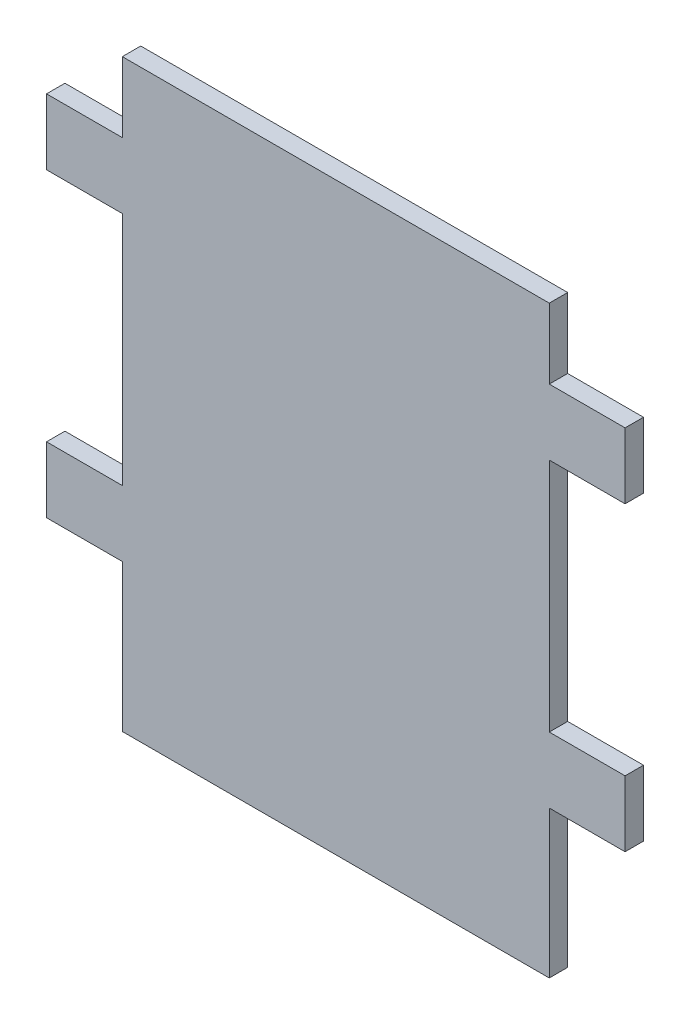
SolidWorks part; units mm, degrees
ref_plane "Front" through (0, 0, 0) normal (0, 0, 1) x (1, 0, 0)
ref_plane "Top" through (0, 0, 0) normal (0, 1, 0) x (1, 0, 0)
ref_plane "Right" through (0, 0, 0) normal (1, 0, 0) x (0, 0, -1)
sketch "Sketch1" plane through (0, 0, 0) normal (0, 0, 1) x (1, 0, 0)
  line L1 (-48.6696, 65.3947) -> (51.1504, 65.3947)
  line L2 (-48.6696, 65.3947) -> (-48.6696, -35.4453)
  line L3 (-48.6696, -35.4453) -> (51.1504, -35.4453)
  line L4 (51.1504, 65.3947) -> (51.1504, -35.4453)
extrude "Boss-Extrude1" add sketch "Sketch1" along normal blind 3.175
sketch "Sketch3" plane through (0, 0, 3.175) normal (0, 0, 1) x (1, 0, 0)
  line L0 (-48.6696, 65.3947) -> (-48.6696, -35.4453) construction
  line L1 (-48.6696, 65.3947) -> (-35.5896, 65.3947)
  line L2 (-48.6696, 65.3947) -> (-48.6696, 53.2946)
  line L3 (-48.6696, 53.2946) -> (-35.5896, 53.2946)
  line L4 (-35.5896, 65.3947) -> (-35.5896, 53.2946)
  line L5 (51.1504, 65.3947) -> (-48.6696, 65.3947) construction
  line L6 (38.0704, 65.3947) -> (51.1504, 65.3947)
  line L7 (-48.6696, 41.9447) -> (-35.5896, 41.9447)
  line L8 (-48.6696, 41.9447) -> (-48.6696, 1.3047)
  line L9 (-48.6696, 1.3047) -> (-35.5896, 1.3047)
  line L10 (-35.5896, 41.9447) -> (-35.5896, 1.3047)
  line L11 (-48.6696, -35.4453) -> (-35.5896, -35.4453)
  line L12 (-48.6696, -35.4453) -> (-48.6696, -10.0453)
  line L13 (-48.6696, -10.0453) -> (-35.5896, -10.0453)
  line L14 (-35.5896, -35.4453) -> (-35.5896, -10.0453)
  line L15 (38.0704, 65.3947) -> (38.0704, 53.2946)
  line L16 (38.0704, 53.2946) -> (51.1504, 53.2946)
  line L17 (51.1504, 65.3947) -> (51.1504, 53.2946)
  line L18 (38.0704, 41.9447) -> (51.1504, 41.9447)
  line L19 (38.0704, 41.9447) -> (38.0704, 1.3047)
  line L20 (38.0704, 1.3047) -> (51.1504, 1.3047)
  line L21 (51.1504, 41.9447) -> (51.1504, 1.3047)
  line L22 (38.0704, -35.4453) -> (51.1504, -35.4453)
  line L23 (38.0704, -35.4453) -> (38.0704, -10.0453)
  line L24 (38.0704, -10.0453) -> (51.1504, -10.0453)
  line L25 (51.1504, -35.4453) -> (51.1504, -10.0453)
  line L26 (-48.6696, -35.4453) -> (51.1504, -35.4453) construction
  line L27 (51.1504, -35.4453) -> (51.1504, 65.3947) construction
  dimension "D1" = 11.35
  dimension "D2" = 12.1
  dimension "D3" = 40.64
  dimension "D4" = 11.35
  dimension "D5" = 11.35
  dimension "D6" = 13.08
extrude "Cut-Extrude1" cut sketch "Sketch3" against normal blind 3.175
